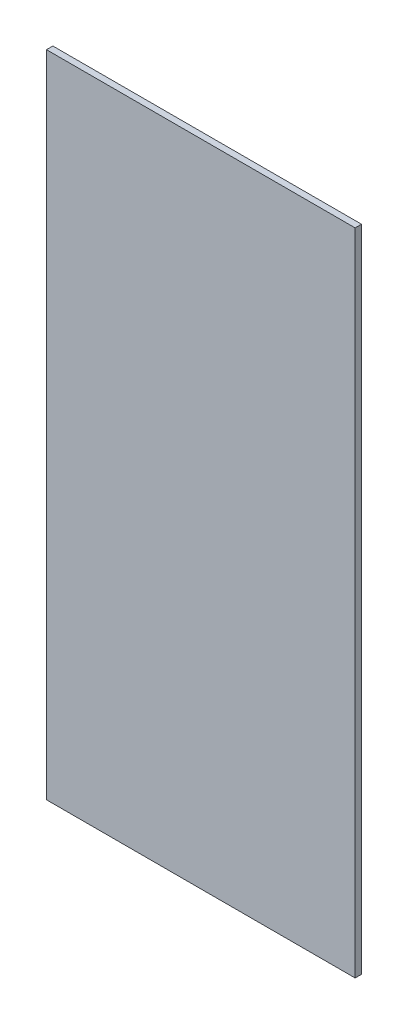
SolidWorks part; units mm, degrees
material "Pine"
ref_plane "Front Plane" through (0, 0, 0) normal (0, 0, 1) x (1, 0, 0)
ref_plane "Top Plane" through (0, 0, 0) normal (0, 1, 0) x (1, 0, 0)
ref_plane "Right Plane" through (0, 0, 0) normal (1, 0, 0) x (0, 0, -1)
sketch "Sketch1" plane through (0, 0, 0) normal (0, 0, 1) x (1, 0, 0)
  line L1 (-134.1966, 367.9592) -> (442.0659, 367.9592)
  line L2 (-134.1966, 367.9592) -> (-134.1966, -844.8908)
  line L3 (-134.1966, -844.8908) -> (442.0659, -844.8908)
  line L4 (442.0659, 367.9592) -> (442.0659, -844.8908)
  dimension "D1" = 576.2625
  dimension "D2" = 1212.85
extrude "Boss-Extrude1" add sketch "Sketch1" along normal blind 11.9062
